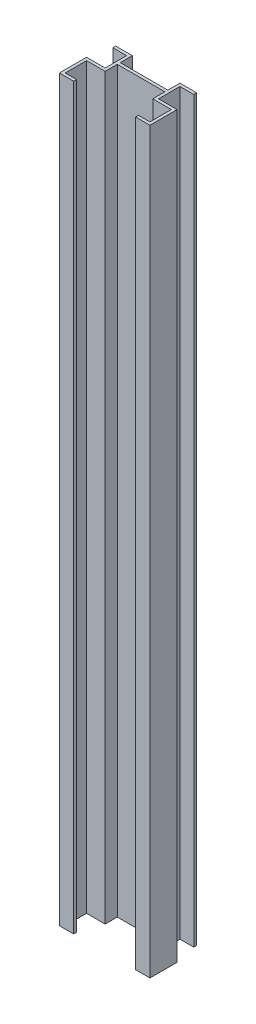
SolidWorks part; units mm, degrees
ref_plane "Front Plane" through (0, 0, 0) normal (0, 0, 1) x (1, 0, 0)
ref_plane "Top Plane" through (0, 0, 0) normal (0, 1, 0) x (1, 0, 0)
ref_plane "Right Plane" through (0, 0, 0) normal (1, 0, 0) x (0, 0, -1)
ref_plane "Plane1" through (0, 0, -76.5) normal (0, 0, -1) x (-1, 0, 0)
sketch "Sketch1" plane through (0, 0, -76.5) normal (0, 0, -1) x (-1, 0, 0)
  line L0 (-95, 0) -> (-50, 0)
  line L1 (-50, 0) -> (-50, 2350)
  line L2 (-50, 2350) -> (-95, 2350)
  line L3 (-95, 2350) -> (-95, 0)
extrude "Boss-Extrude1" add sketch "Sketch1" against normal blind 31.5
sketch "Sketch2" plane through (50, 0, 0) normal (-1, 0, 0) x (0, 0, 1)
  line L0 (-70.5, 0) -> (-76.5, 0)
  line L1 (-76.5, 0) -> (-76.5, 2350)
  line L2 (-76.5, 2350) -> (-70.5, 2350)
  line L3 (-70.5, 2350) -> (-70.5, 0)
extrude "Boss-Extrude2" add sketch "Sketch2" along normal blind 145
sketch "Sketch3" plane through (0, 0, -70.5) normal (0, 0, 1) x (1, 0, 0)
  line L0 (-50, 0) -> (-95, 0)
  line L1 (-95, 0) -> (-95, 2350)
  line L2 (-95, 2350) -> (-50, 2350)
  line L3 (-50, 2350) -> (-50, 0)
extrude "Boss-Extrude3" add sketch "Sketch3" along normal blind 76.5
sketch "Sketch4" plane through (0, 0, -45) normal (0, 0, 1) x (1, 0, 0)
  line L0 (89, 2350) -> (95, 2350)
  line L1 (95, 2350) -> (95, 0)
  line L2 (95, 0) -> (89, 0)
  line L3 (89, 0) -> (89, 2350)
extrude "Boss-Extrude4" add sketch "Sketch4" along normal blind 51
sketch "Sketch5" plane through (89, 0, 0) normal (-1, 0, 0) x (0, 0, 1)
  line L0 (6, 0) -> (0, 0)
  line L1 (0, 0) -> (0, 2350)
  line L2 (0, 2350) -> (6, 2350)
  line L3 (6, 2350) -> (6, 0)
extrude "Boss-Extrude5" add sketch "Sketch5" along normal blind 24
sketch "Sketch6" plane through (0, 0, 6) normal (0, 0, 1) x (1, 0, 0)
  line L0 (-65, 2350) -> (-65, 0)
  line L1 (-65, 0) -> (-50, 0)
  line L2 (-50, 0) -> (-50, 2350)
  line L3 (-50, 2350) -> (-65, 2350)
extrude "Cut-Extrude1" cut sketch "Sketch6" against normal blind 6
sketch "Sketch7" plane through (0, 0, 0) normal (0, 0, 1) x (1, 0, 0)
  line L0 (-89, 0) -> (-50, 0)
  line L1 (-50, 0) -> (-50, 2350)
  line L2 (-50, 2350) -> (-89, 2350)
  line L3 (-89, 2350) -> (-89, 0)
extrude "Cut-Extrude2" cut sketch "Sketch7" against normal blind 45
sketch "Sketch8" plane through (0, 2350, 0) normal (0, 1, 0) x (-1, 0, 0)
  line L0 (50, -76.5) -> (50, -70.5)
  line L1 (50, -70.5) -> (-50, -70.5)
  line L2 (-50, -70.5) -> (-50, -76.5)
  line L3 (-50, -76.5) -> (50, -76.5)
extrude "Cut-Extrude3" cut sketch "Sketch8" against normal blind 100
sketch "Sketch9" plane through (0, 0, -76.5) normal (0, 0, -1) x (-1, 0, 0)
  line L0 (-95, 2350) -> (-50, 2350)
  line L1 (-50, 2350) -> (-50, 0)
  line L2 (-50, 0) -> (-95, 0)
  line L3 (-95, 0) -> (-95, 2350)
extrude "Boss-Extrude6" add sketch "Sketch9" along normal blind 25.5
sketch "Sketch10" plane through (0, 0, 0) normal (0, -1, 0) x (1, 0, 0)
  line L0 (95, -102) -> (95, -51)
  line L1 (95, -51) -> (56, -51)
  line L2 (56, -51) -> (56, -102)
  line L3 (56, -102) -> (95, -102)
extrude "Cut-Extrude4" cut sketch "Sketch10" against normal through all
sketch "Sketch11" plane through (56, 0, 0) normal (1, 0, 0) x (0, 0, -1)
  line L0 (102, 0) -> (96, 0)
  line L1 (96, 0) -> (96, 2350)
  line L2 (96, 2350) -> (102, 2350)
  line L3 (102, 2350) -> (102, 0)
extrude "Boss-Extrude7" add sketch "Sketch11" along normal blind 29
sketch "Sketch12" plane through (0, 0, -76.5) normal (0, 0, -1) x (-1, 0, 0)
  line L0 (95, 0) -> (50, 0)
  line L1 (50, 0) -> (50, 2350)
  line L2 (50, 2350) -> (95, 2350)
  line L3 (95, 2350) -> (95, 0)
extrude "Boss-Extrude8" add sketch "Sketch12" along normal blind 25.5
sketch "Sketch13" plane through (0, 2350, 0) normal (0, 1, 0) x (-1, 0, 0)
  line L0 (95, -51) -> (56, -51)
  line L1 (56, -51) -> (56, -102)
  line L2 (56, -102) -> (95, -102)
  line L3 (95, -102) -> (95, -51)
extrude "Cut-Extrude5" cut sketch "Sketch13" against normal through all
sketch "Sketch14" plane through (-56, 0, 0) normal (-1, 0, 0) x (0, 0, 1)
  line L0 (-96, 0) -> (-102, 0)
  line L1 (-102, 0) -> (-102, 2350)
  line L2 (-102, 2350) -> (-96, 2350)
  line L3 (-96, 2350) -> (-96, 0)
extrude "Boss-Extrude9" add sketch "Sketch14" along normal blind 29
hole_wizard "Ø10.0 (10) Diameter Hole1" positions "Sketch16" profile "Sketch15" hole size "Ø10.0" standard "ANSI Metric"
sketch "Sketch16" plane through (-56, 0, 0) normal (-1, 0, 0) x (0, 0, 1)
  point P0 (-73.5, 2330)
sketch "Sketch15" plane through (-56, 2330, -73.5) normal (0, 1, 0) x (0, 0, 1)
  line L0 (0, 0) -> (0, 6)
  line L1 (0, 6) -> (5, 6)
  line L2 (5, 6) -> (5, 0)
  line L5 (5, 0) -> (0, 0)
  line L11 (0, -6.35) -> (0, 107.95) construction
  dimension "Thru Hole Dia." = 10
  dimension "Thru Hole Depth" = 6
hole_wizard "Ø10.0 (10) Diameter Hole2" positions "Sketch18" profile "Sketch17" hole size "Ø10.0" standard "ANSI Metric"
sketch "Sketch18" plane through (50, 0, 0) normal (-1, 0, 0) x (0, 0, 1)
  point P0 (-73.5, 2330)
sketch "Sketch17" plane through (50, 2330, -73.5) normal (0, 1, 0) x (0, 0, 1)
  line L0 (0, 0) -> (0, 45)
  line L1 (0, 45) -> (5, 45)
  line L2 (5, 45) -> (5, 0)
  line L5 (5, 0) -> (0, 0)
  line L11 (0, -6.35) -> (0, 107.95) construction
  dimension "Thru Hole Dia." = 10
  dimension "Thru Hole Depth" = 45
sketch "Sketch24" plane through (0, 2350, 0) normal (0, 1, 0) x (1, 0, 0)
  line L1 (-140.6741, 122.2057) -> (147.1884, 122.2057)
  line L2 (-140.6741, 122.2057) -> (-140.6741, -41.0365)
  line L3 (-140.6741, -41.0365) -> (147.1884, -41.0365)
  line L4 (147.1884, 122.2057) -> (147.1884, -41.0365)
extrude "Cut-Extrude8" cut sketch "Sketch24" against normal blind 800
